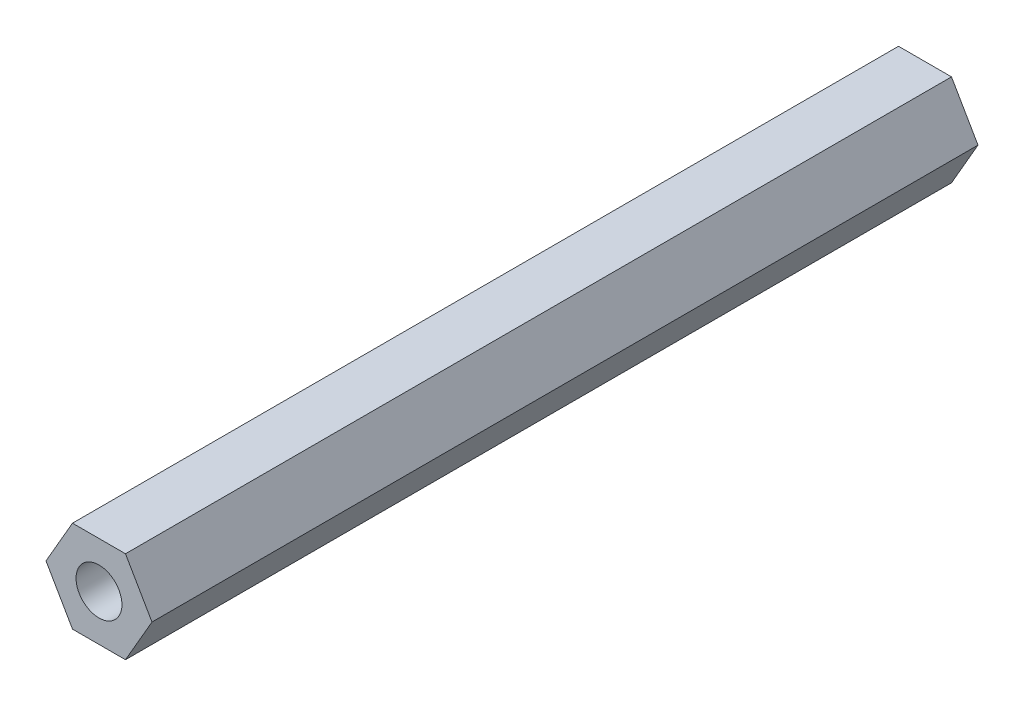
SolidWorks part; units mm, degrees
material "6061 合金"
ref_plane "前视基准面" through (0, 0, 0) normal (0, 0, 1) x (1, 0, 0)
ref_plane "上视基准面" through (0, 0, 0) normal (0, 1, 0) x (1, 0, 0)
ref_plane "右视基准面" through (0, 0, 0) normal (1, 0, 0) x (0, 0, -1)
sketch "草图1" plane through (0, 0, 0) normal (0, 0, 1) x (1, 0, 0)
  line L1 (1.4434, 2.5) -> (-1.4434, 2.5)
  line L2 (-1.4434, 2.5) -> (-2.8868, 0)
  line L3 (-2.8868, 0) -> (-1.4434, -2.5)
  line L4 (-1.4434, -2.5) -> (1.4434, -2.5)
  line L5 (1.4434, -2.5) -> (2.8868, 0)
  line L6 (2.8868, 0) -> (1.4434, 2.5)
  circle A0 centre (0, 0) radius 2.5 construction
  dimension "D1" = 5
extrude "凸台-拉伸1" add sketch "草图1" along normal blind 45
hole_wizard "M3 螺纹孔1" positions "草图2" profile "草图3" tap size "M3" standard "GB" end condition through all
sketch "草图2" plane through (0, 0, 45) normal (0, 0, 1) x (1, 0, 0)
  point P0 (0, 0)
sketch "草图3" plane through (0, 0, 45) normal (1, 0, 0) x (0, -1, 0)
  line L0 (0, 0) -> (0, 45)
  line L1 (0, 45) -> (1.25, 45)
  line L2 (1.25, 45) -> (1.25, 0)
  line L5 (1.25, 0) -> (0, 0)
  line L11 (0, -6.35) -> (0, 107.95) construction
  dimension "通孔螺纹孔钻头直径" = 2.5
  dimension "通孔螺纹孔钻头深度" = 45
cosmetic thread "孔螺蚊线1" parameters "D2"=3
